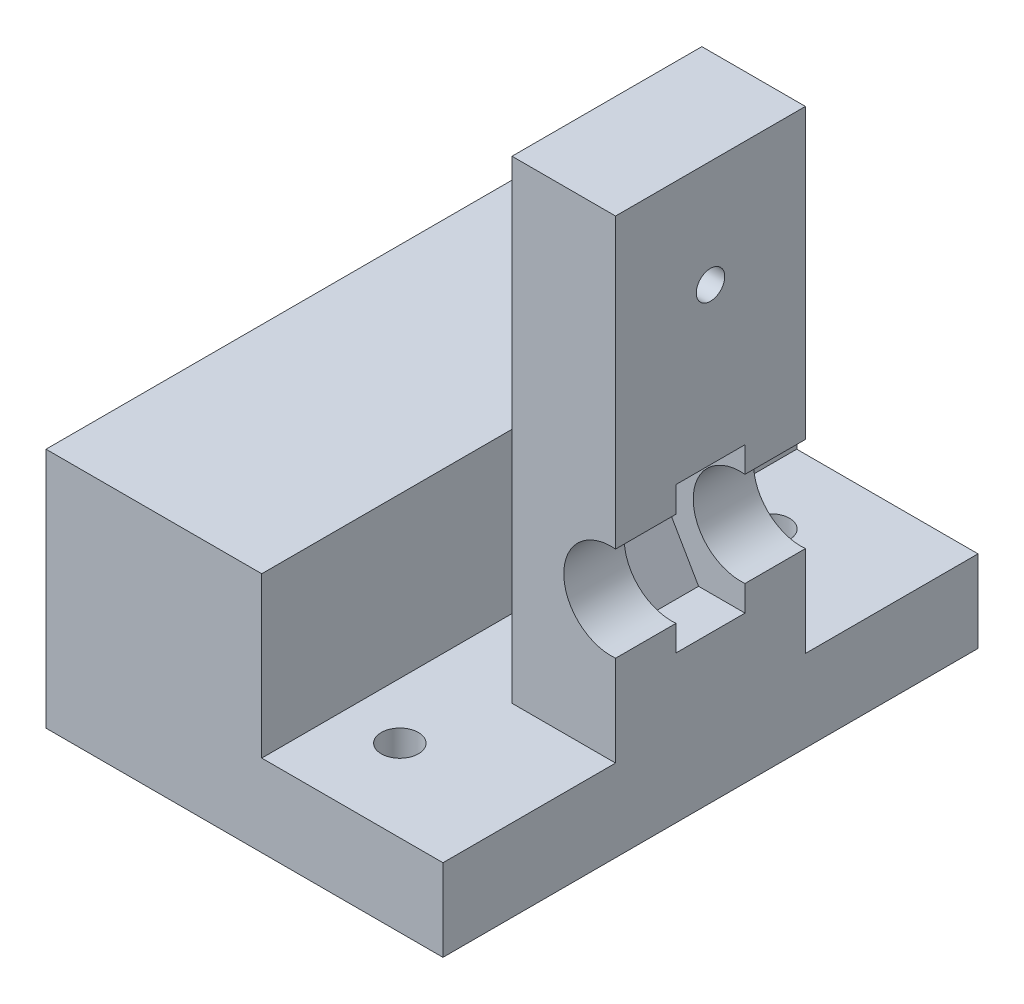
SolidWorks part; units mm, degrees
ref_plane "前基準面" through (0, 0, 0) normal (0, 0, 1) x (1, 0, 0)
ref_plane "上基準面" through (0, 0, 0) normal (0, 1, 0) x (1, 0, 0)
ref_plane "右基準面" through (0, 0, 0) normal (1, 0, 0) x (0, 0, -1)
sketch "草圖1" plane through (0, 0, 0) normal (0, 0, 1) x (1, 0, 0)
  line L0 (-0.3675, -59.7793) -> (-0.3675, -34.2793) construction
  line L1 (-11.8675, 4.6207) -> (11.1325, 4.6207)
  line L2 (-11.8675, 4.6207) -> (-11.8675, -59.7793)
  line L3 (-11.8675, -59.7793) -> (11.1325, -59.7793)
  line L4 (11.1325, 4.6207) -> (11.1325, -59.7793)
  line L5 (-7.6854, -30.0543) -> (6.9504, -38.5043) construction
  line L6 (9.3897, -34.2793) -> (4.5111, -25.8293)
  line L7 (4.5111, -25.8293) -> (-5.2461, -25.8293)
  line L8 (-5.2461, -25.8293) -> (-10.1247, -34.2793)
  line L9 (-10.1247, -34.2793) -> (-5.2461, -42.7293)
  line L10 (-5.2461, -42.7293) -> (4.5111, -42.7293)
  line L11 (4.5111, -42.7293) -> (9.3897, -34.2793)
  circle A0 centre (-0.3675, -34.2793) radius 8.45 construction
  dimension "D1" = 23
  dimension "D2" = 64.4
  dimension "D3" = 25.5
  dimension "D4" = 16.9
extrude "填料-伸長1" add sketch "草圖1" along normal blind 8
sketch "草圖3" plane through (0, 0, 8) normal (0, 0, 1) x (1, 0, 0)
  line L0 (-0.3675, -59.7793) -> (-0.3675, -34.2793) construction
  line L1 (-11.8675, 4.6207) -> (11.1325, 4.6207)
  line L2 (-11.8675, 4.6207) -> (-11.8675, -59.7793)
  line L3 (-11.8675, -59.7793) -> (11.1325, -59.7793)
  line L4 (11.1325, 4.6207) -> (11.1325, -59.7793)
  circle A0 centre (-0.3675, -34.2793) radius 5.5
  dimension "D1" = 25.5
extrude "填料-伸長2" add sketch "草圖3" along normal blind 7
sketch "草圖4" plane through (0, 0, 0) normal (0, 0, -1) x (-1, 0, 0)
  line L0 (0.3675, -59.7793) -> (0.3675, -34.2793) construction
  line L1 (-11.1325, 4.6207) -> (11.8675, 4.6207)
  line L2 (-11.1325, 4.6207) -> (-11.1325, -59.7793)
  line L3 (-11.1325, -59.7793) -> (11.8675, -59.7793)
  line L4 (11.8675, 4.6207) -> (11.8675, -59.7793)
  circle A0 centre (0.3675, -34.2793) radius 5.5
extrude "填料-伸長3" add sketch "草圖4" along normal blind 7
sketch "草圖5" plane through (11.1325, 0, 0) normal (1, 0, 0) x (0, 0, -1)
  line L0 (-4, -59.7793) -> (-4, -7.7793) construction
  line L1 (-15, -59.7793) -> (7, -59.7793) construction
  circle A0 centre (-4, -7.7793) radius 1.65
  dimension "D2" = 3.3
  dimension "D1" = 52
extrude "除料-伸長1" cut sketch "草圖5" against normal through all
sketch "草圖6" plane through (11.1325, 0, 0) normal (1, 0, 0) x (0, 0, -1)
  line L1 (-15, 4.6207) -> (7, 4.6207)
  line L2 (-15, 4.6207) -> (-15, -59.7793)
  line L3 (-15, -59.7793) -> (7, -59.7793)
  line L4 (7, 4.6207) -> (7, -59.7793)
extrude "除料-伸長2" cut sketch "草圖6" against normal blind 11
sketch "草圖7" plane through (0, -59.7793, 0) normal (0, -1, 0) x (1, 0, 0)
  line L0 (0.1325, 15) -> (0.1325, 35)
  line L1 (0.1325, 35) -> (-45.8675, 35)
  line L2 (0.1325, -7) -> (0.1325, -27)
  line L3 (0.1325, -27) -> (-45.8675, -27)
  line L4 (-45.8675, -27) -> (-45.8675, 35)
  line L5 (0.1325, 15) -> (0.1325, -7)
  dimension "D1" = 46
  dimension "D2" = 62
extrude "填料-伸長4" add sketch "草圖7" against normal blind 9.5
sketch "草圖8" plane through (0, -50.2793, 0) normal (0, 1, 0) x (1, 0, 0)
  line L0 (-45.8675, -35) -> (-14.3675, -35) construction
  line L1 (0.1325, -35) -> (-45.8675, -35) construction
  line L2 (-14.3675, -35) -> (-14.3675, -25.5) construction
  line L3 (-14.3675, -25.5) -> (-45.8675, -25.5) construction
  line L4 (-45.8675, -35) -> (-45.8675, 27) construction
  line L5 (-45.8675, -25.5) -> (-45.8675, -35) construction
  line L6 (-45.8675, 27) -> (-14.3675, 27) construction
  line L7 (-45.8675, 27) -> (0.1325, 27) construction
  line L8 (-14.3675, 27) -> (-14.3675, 17.5) construction
  line L9 (-14.3675, 17.5) -> (-45.8675, 17.5) construction
  line L10 (-45.8675, 17.5) -> (-45.8675, 27) construction
  circle A0 centre (-14.3675, 17.5) radius 2.15
  circle A1 centre (-14.3675, -25.5) radius 2.15
  dimension "D1" = 31.5
  dimension "D5" = 4.3
  dimension "D6" = 4.3
  dimension "D2" = 9.5
  dimension "D3" = 31.5
  dimension "D4" = 9.5
extrude "除料-伸長3" cut sketch "草圖8" against normal through all
sketch "草圖9" plane through (0, -59.7793, 0) normal (0, -1, 0) x (1, 0, 0)
  line L0 (-45.8675, 35) -> (-34.0675, 35) construction
  line L1 (0.1325, 35) -> (-45.8675, 35) construction
  line L2 (-34.0675, 35) -> (-34.0675, 23.2) construction
  line L3 (-34.0675, 23.2) -> (-45.8675, 23.2) construction
  line L4 (-45.8675, 35) -> (-45.8675, -27) construction
  line L5 (-45.8675, 23.2) -> (-45.8675, 35) construction
  line L6 (-45.8675, -27) -> (-45.8675, -15.2) construction
  line L7 (-45.8675, -15.2) -> (-34.0675, -15.2) construction
  line L8 (-34.0675, -15.2) -> (-34.0675, -27) construction
  line L9 (-45.8675, -27) -> (0.1325, -27) construction
  line L10 (-34.0675, -27) -> (-45.8675, -27) construction
  circle A0 centre (-34.0675, 23.2) radius 4.75
  circle A1 centre (-34.0675, -15.2) radius 4.75
  dimension "D1" = 11.8
  dimension "D5" = 9.5
  dimension "D6" = 9.5
  dimension "D2" = 11.8
  dimension "D3" = 11.8
  dimension "D4" = 11.8
extrude "除料-伸長4" cut sketch "草圖9" against normal blind 3.5
sketch "草圖10" plane through (0, -50.2793, 0) normal (0, 1, 0) x (1, 0, 0)
  line L0 (0.1325, -35) -> (-45.8675, -35) construction
  line L1 (-45.8675, 27) -> (-20.8675, 27)
  line L2 (-45.8675, 27) -> (-45.8675, -35)
  line L3 (-45.8675, -35) -> (-20.8675, -35)
  line L4 (-20.8675, 27) -> (-20.8675, -35)
  dimension "D1" = 25
extrude "填料-伸長5" add sketch "草圖10" along normal blind 18.5
sketch "草圖11" plane through (-45.8675, 0, 0) normal (-1, 0, 0) x (0, 0, 1)
  line L0 (4, -31.7793) -> (4, -59.7793) construction
  line L1 (-27, -31.7793) -> (35, -31.7793) construction
  line L2 (35, -59.7793) -> (-27, -59.7793) construction
  line L3 (4, -31.7793) -> (33.95, -31.7793) construction
  line L4 (33.95, -31.7793) -> (33.95, -59.7793) construction
  line L5 (33.95, -59.7793) -> (4, -59.7793) construction
  line L6 (4, -59.7793) -> (-25.95, -59.7793) construction
  line L7 (-25.95, -59.7793) -> (-25.95, -31.7793) construction
  line L8 (-25.95, -31.7793) -> (4, -31.7793) construction
  dimension "D1" = 28
